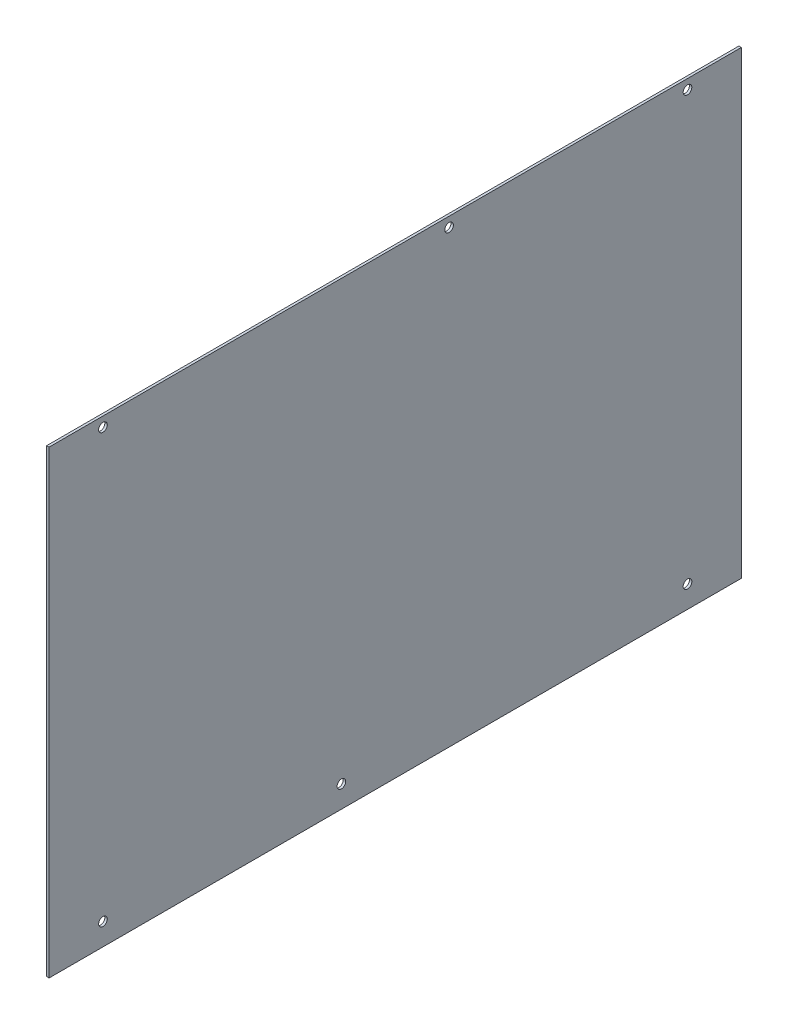
SolidWorks part; units mm, degrees
material "6061-T6 (SS)"
ref_plane "Front Plane" through (0, 0, 0) normal (0, 0, 1) x (1, 0, 0)
ref_plane "Top Plane" through (0, 0, 0) normal (0, 1, 0) x (1, 0, 0)
ref_plane "Right Plane" through (0, 0, 0) normal (1, 0, 0) x (0, 0, -1)
sketch "Sketch2" plane through (0, 0, 0) normal (1, 0, 0) x (0, 0, -1)
  line L0 (0, 0) -> (0, 24.495) construction
  line L1 (-225, 145.4859) -> (225, 145.4859)
  line L2 (-225, 145.4859) -> (-225, -153.4107)
  line L3 (-225, -153.4107) -> (225, -153.4107)
  line L4 (225, 145.4859) -> (225, -153.4107)
  line L5 (0, 0) -> (27.6768, 0) construction
  line L6 (35, 139.1232) -> (35, -139.1232) construction
  line L7 (-190, 139.1232) -> (190, 139.1232) construction
  line L8 (-190, 139.1232) -> (-190, -139.1232) construction
  line L9 (-190, -139.1232) -> (190, -139.1232) construction
  line L10 (190, 139.1232) -> (190, -139.1232) construction
  line L11 (-190, 139.1232) -> (190, -139.1232) construction
  line L12 (-190, -139.1232) -> (190, 139.1232) construction
  line L13 (-35, 139.1232) -> (-35, -139.1232) construction
  point P12 (0, -153.4107)
  dimension "D1" = 380
  dimension "D2" = 278.2464
  dimension "D3" = 6.3627
  dimension "D4" = 14.2875
  dimension "D5" = 450
  dimension "D6" = 35
extrude "Boss-Extrude1" add sketch "Sketch2" along normal blind 1.6002
hole_wizard "#10 Clearance Hole1" positions "Sketch4" profile "Sketch3" hole size "#10" standard "ANSI Inch"
sketch "Sketch4" plane through (0, 0, 0) normal (-1, 0, 0) x (0, 0, 1)
  point P0 (-190, 139.1232)
  point P3 (-35, 139.1232)
  point P6 (190, 139.1232)
  point P9 (190, -139.1232)
  point P12 (35, -139.1232)
  point P15 (-190, -139.1232)
sketch "Sketch3" plane through (0, 139.1232, -190) normal (0, 1, 0) x (0, 0, 1)
  line L0 (0, 0) -> (0, 21.6864)
  line L1 (0, 21.6864) -> (2.8067, 20)
  line L2 (2.8067, 20) -> (2.8067, 0)
  line L5 (2.8067, 0) -> (0, 0)
  line L10 (0, 21.6864) -> (-2.8067, 20) construction
  line L11 (0, -6.35) -> (0, 107.95) construction
  dimension "Hole Dia." = 5.6134
  dimension "Hole Depth" = 20
  dimension "Drill Angle" = 118
